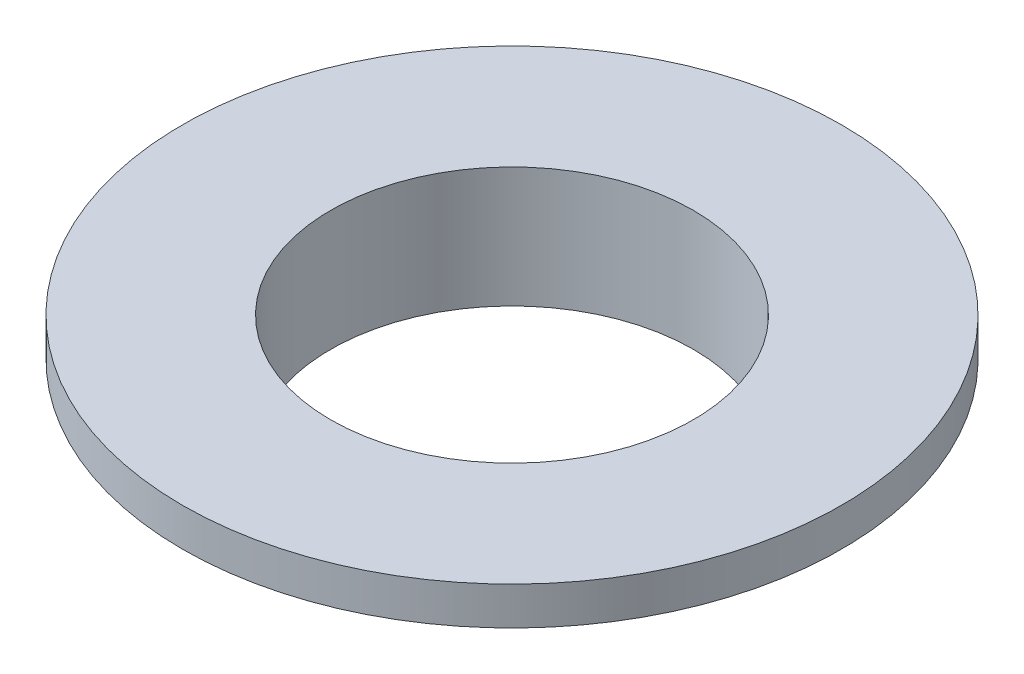
SolidWorks part; units mm, degrees
ref_plane "Front Plane" through (0, 0, 0) normal (0, 0, 1) x (1, 0, 0)
ref_plane "Top Plane" through (0, 0, 0) normal (0, 1, 0) x (1, 0, 0)
ref_plane "Right Plane" through (0, 0, 0) normal (1, 0, 0) x (0, 0, -1)
sketch "Sketch1" plane through (0, 0, 0) normal (0, 1, 0) x (1, 0, 0)
  circle A0 centre (0, 0) radius 13
  dimension "D1" = 26
extrude "Boss-Extrude1" add sketch "Sketch1" along normal blind 1.5
sketch "Sketch2" plane through (0, 0, 0) normal (0, -1, 0) x (1, 0, 0)
  circle A0 centre (0, 0) radius 7.75
  dimension "D1" = 15.5
extrude "Boss-Extrude2" add sketch "Sketch2" along normal blind 3.25
sketch "Sketch3" plane through (0, 1.5, 0) normal (0, 1, 0) x (1, 0, 0)
  circle A0 centre (0, 0) radius 7.1554
  dimension "D1" = 14.3108
extrude "Cut-Extrude1" cut sketch "Sketch3" against normal through all contours A0
